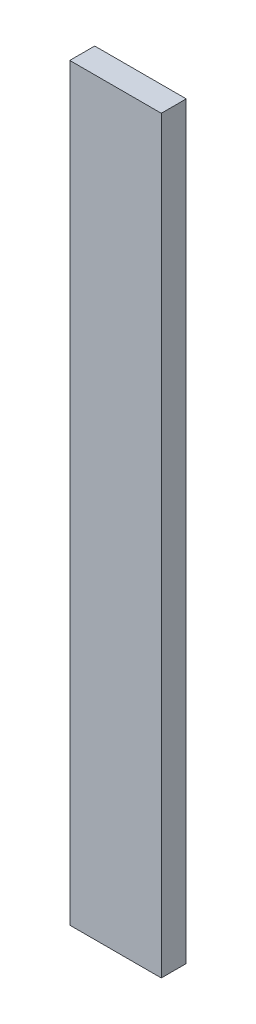
SolidWorks part; units mm, degrees
material "Oak"
ref_plane "Front Plane" through (0, 0, 0) normal (0, 0, 1) x (1, 0, 0)
ref_plane "Top Plane" through (0, 0, 0) normal (0, 1, 0) x (1, 0, 0)
ref_plane "Right Plane" through (0, 0, 0) normal (1, 0, 0) x (0, 0, -1)
sketch "Sketch1" plane through (0, 0, 0) normal (0, 1, 0) x (1, 0, 0)
  line L1 (-69.85, -19.05) -> (69.85, -19.05)
  line L2 (-69.85, -19.05) -> (-69.85, 19.05)
  line L3 (-69.85, 19.05) -> (69.85, 19.05)
  line L4 (69.85, -19.05) -> (69.85, 19.05)
  line L5 (-69.85, -19.05) -> (69.85, 19.05) construction
  line L6 (-69.85, 19.05) -> (69.85, -19.05) construction
  point P0 (0, 0)
  dimension "D1" = 38.1
  dimension "D2" = 139.7
extrude "Boss-Extrude1" add sketch "Sketch1" along normal blind 1143 contours L1 L4 L3 L2
